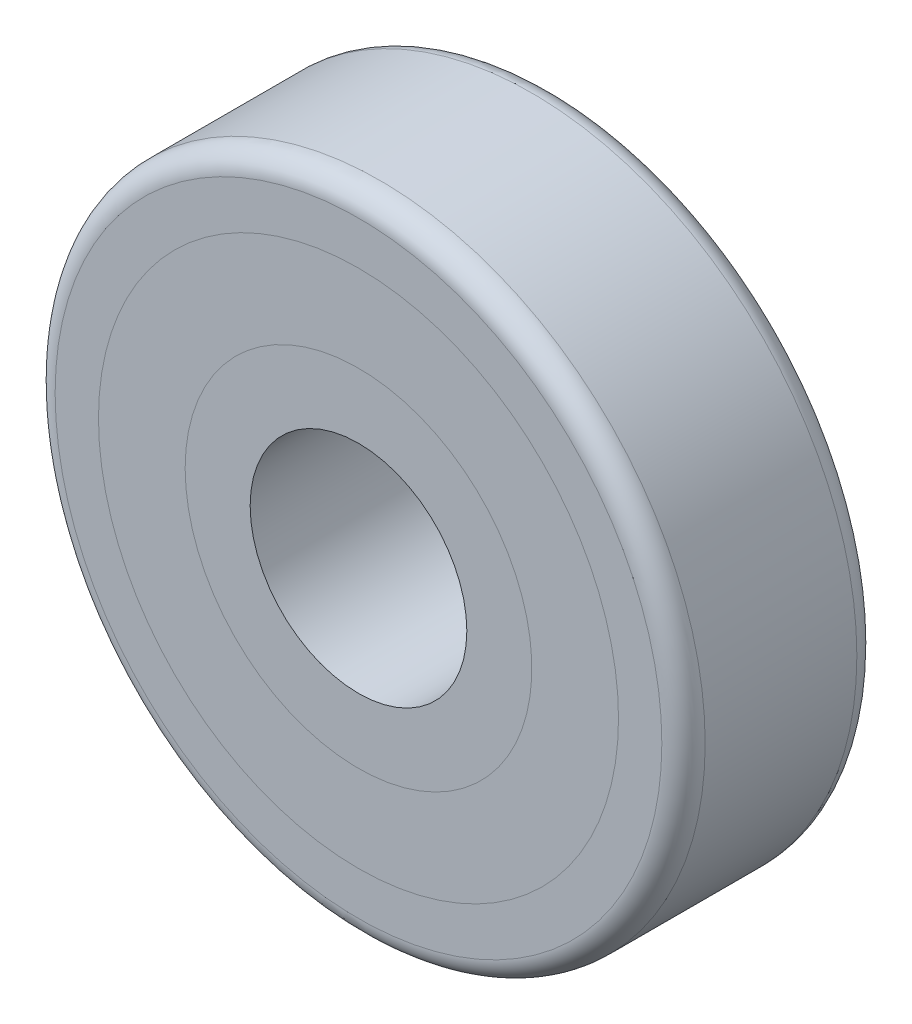
SolidWorks part; units mm, degrees
ref_plane "Front Plane" through (0, 0, 0) normal (0, 0, 1) x (1, 0, 0)
ref_plane "Top Plane" through (0, 0, 0) normal (0, 1, 0) x (1, 0, 0)
ref_plane "Right Plane" through (0, 0, 0) normal (1, 0, 0) x (0, 0, -1)
sketch "Sketch1" plane through (0, 0, 0) normal (0, 0, 1) x (1, 0, 0)
  circle A0 centre (0, 0) radius 15
  circle A1 centre (0, 0) radius 12
  dimension "D1" = 30
  dimension "D2" = 24
extrude "Boss-Extrude1" add sketch "Sketch1" along normal blind 9
sketch "Sketch2" plane through (0, 0, 0) normal (0, 0, -1) x (-1, 0, 0)
  circle A0 centre (0, 0) radius 8
  circle A1 centre (0, 0) radius 5
  dimension "D1" = 16
  dimension "D2" = 10
extrude "Boss-Extrude2" add sketch "Sketch2" against normal blind 9 separate body
sketch "Sketch3" plane through (0, 0, 0) normal (0, 0, -1) x (-1, 0, 0)
  circle A0 centre (0, 0) radius 12
  circle A1 centre (0, 0) radius 8
  dimension "D1" = 24
  dimension "D2" = 16
extrude "Boss-Extrude3" add sketch "Sketch3" against normal blind 9 separate body
fillet "Fillet1" radius 1 2 edges at (15, 0, 9) (15, 0, 0)
